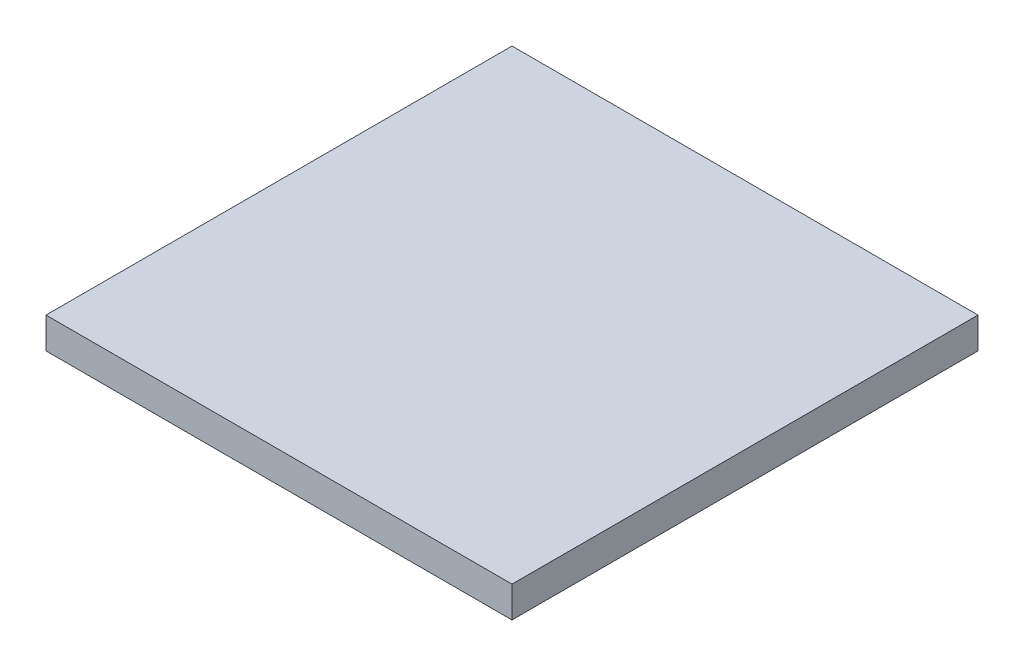
SolidWorks part; units mm, degrees
ref_plane "Front Plane" through (0, 0, 0) normal (0, 0, 1) x (1, 0, 0)
ref_plane "Top Plane" through (0, 0, 0) normal (0, 1, 0) x (1, 0, 0)
ref_plane "Right Plane" through (0, 0, 0) normal (1, 0, 0) x (0, 0, -1)
sketch "Sketch1" plane through (0, 0, 0) normal (0, 1, 0) x (1, 0, 0)
  line L1 (-15, 15) -> (15, 15)
  line L2 (-15, 15) -> (-15, -15)
  line L3 (-15, -15) -> (15, -15)
  line L4 (15, 15) -> (15, -15)
  line L5 (-15, 15) -> (15, -15) construction
  line L6 (-15, -15) -> (15, 15) construction
  point P0 (0, 0)
  dimension "D1" = 30
extrude "Boss-Extrude1" add sketch "Sketch1" along normal blind 2
